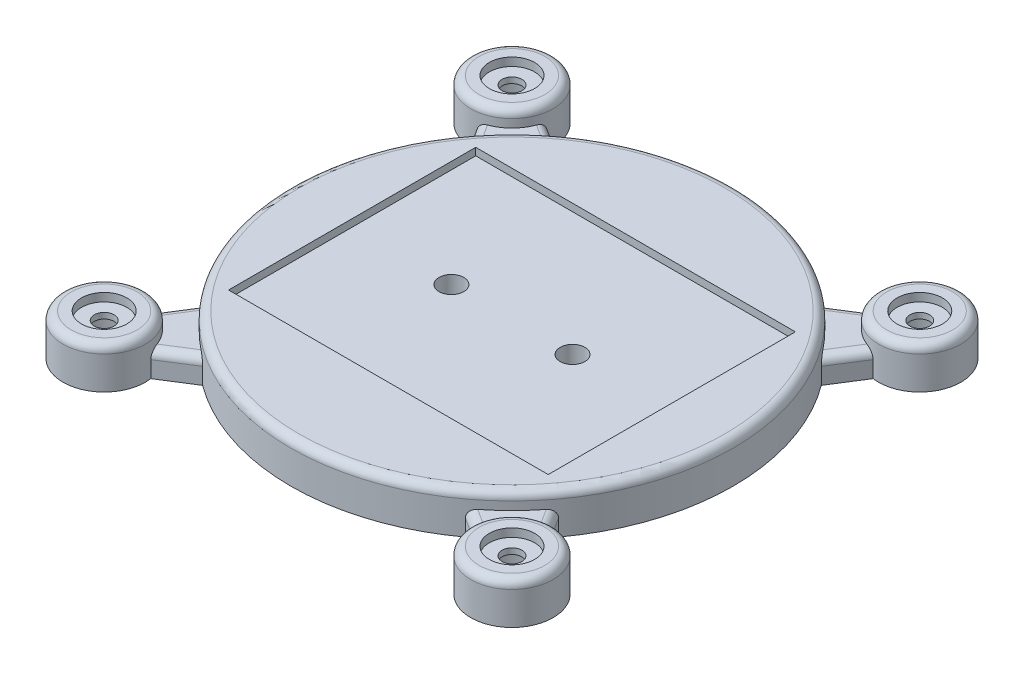
SolidWorks part; units mm, degrees
material "ABS"
ref_plane "Front Plane" through (0, 0, 0) normal (0, 0, 1) x (1, 0, 0)
ref_plane "Top Plane" through (0, 0, 0) normal (0, 1, 0) x (1, 0, 0)
ref_plane "Right Plane" through (0, 0, 0) normal (1, 0, 0) x (0, 0, -1)
sketch "Sketch1" plane through (0, 0, 0) normal (0, 1, 0) x (1, 0, 0)
  circle A0 centre (0, 0) radius 26.85
  dimension "D1" = 53.7
extrude "Boss-Extrude1" add sketch "Sketch1" along normal blind 5
fillet "Fillet1" radius 1 1 edges at (0, 5, 26.85)
sketch "Sketch2" plane through (0, 5, 0) normal (0, 1, 0) x (1, 0, 0)
  line L1 (-19.4, 15) -> (19.4, 15)
  line L2 (-19.4, 15) -> (-19.4, -15)
  line L3 (-19.4, -15) -> (19.4, -15)
  line L4 (19.4, 15) -> (19.4, -15)
  line L5 (-19.4, 15) -> (19.4, -15) construction
  line L6 (-19.4, -15) -> (19.4, 15) construction
  point P0 (0, 0)
  dimension "D1" = 38.8
  dimension "D2" = 30
extrude "Cut-Extrude1" cut sketch "Sketch2" against normal blind 0.9
sketch "Sketch3" plane through (0, 4.1, 0) normal (0, 1, 0) x (1, 0, 0)
  line L0 (-2.75, 0) -> (2.75, 0) construction
  circle A0 centre (7.35, 0) radius 1.5
  circle A1 centre (-7.35, 0) radius 1.5
  dimension "D1" = 3
  dimension "D3" = 3
  dimension "D2" = 7.35
  dimension "D4" = 7.35
extrude "Cut-Extrude2" cut sketch "Sketch3" against normal through all
sketch "Sketch5" plane through (0, 0, 0) normal (0, 1, 0) x (1, 0, 0)
  line L0 (0, 0) -> (24.7487, -24.7487)
  line L1 (-2.75, 0) -> (2.75, 0) construction
  circle A0 centre (24.7487, -24.7487) radius 5
  circle A1 centre (-24.7487, -24.7487) radius 5
  circle A2 centre (-24.7487, 24.7487) radius 5
  circle A3 centre (24.7487, 24.7487) radius 5
  point P15 (0, 0)
  dimension "D2" = 10
  dimension "D1" = 35
  dimension "D3" = 45
  dimension "D4" = 4
sketch "Sketch6" plane through (0, 0, 0) normal (0, 1, 0) x (1, 0, 0)
  line L8 (24.0416, -19.799) -> (21.6024, -15.9455)
  line L9 (19.799, -24.0416) -> (15.9455, -21.6024)
  arc A2 (15.9455, -21.6024) -> (21.6024, -15.9455) centre (0, 0) ccw
  arc A3 (24.0416, -19.799) -> (19.799, -24.0416) centre (24.7487, -24.7487) ccw
  dimension "D2" = 35
  dimension "D1" = 53.7
  dimension "D4" = 10
  dimension "D5" = 8
  dimension "D7" = 6
extrude "Boss-Extrude4" add sketch "Sketch5" along normal blind 5 separate body
extrude "Boss-Extrude5" add sketch "Sketch6" along normal blind 3
fillet "Fillet5" radius 1 2 edges at (22.822, 3, 17.8723) (17.8723, 3, 22.822)
pattern_circular "CirPattern20" count 4 over 360 about axis through (0, 0, 0) along (0, 1, 0) of "Fillet5", "Boss-Extrude5"
fillet "Fillet6" radius 1 1 edges at (-24.7487, 5, -19.7487)
fillet "Fillet7" radius 1 1 edges at (24.7487, 5, -19.7487)
fillet "Fillet8" radius 1 1 edges at (-24.7487, 5, 29.7487)
fillet "Fillet9" radius 1 1 edges at (24.7487, 5, 29.7487)
sketch "Sketch9" plane through (0, 5, 0) normal (0, 1, 0) x (1, 0, 0)
  line L0 (0, 0) -> (24.7487, -24.7487) construction
  line L1 (-2.75, 0) -> (2.75, 0) construction
  circle A0 centre (24.7487, -24.7487) radius 2.75
  circle A1 centre (-24.7487, -24.7487) radius 2.75
  circle A2 centre (-24.7487, 24.7487) radius 2.75
  circle A3 centre (24.7487, 24.7487) radius 2.75
  point P15 (0, 0)
  dimension "D3" = 5.5
  dimension "D1" = 35
  dimension "D2" = 45
  dimension "D4" = 4
extrude "Cut-Extrude5" cut sketch "Sketch9" against normal blind 1
sketch "Sketch10" plane through (0, 4, 0) normal (0, 1, 0) x (1, 0, 0)
  line L0 (0, 0) -> (24.7487, -24.7487) construction
  circle A0 centre (24.7487, -24.7487) radius 1.2
  circle A1 centre (-24.7487, -24.7487) radius 1.2
  circle A2 centre (-24.7487, 24.7487) radius 1.2
  circle A3 centre (24.7487, 24.7487) radius 1.2
  point P14 (0, 0)
  dimension "D1" = 2.4
  dimension "D2" = 4
extrude "Cut-Extrude6" cut sketch "Sketch10" against normal through all
sketch "Sketch11" plane through (0, 0, 0) normal (0, -1, 0) x (1, 0, 0)
  line L0 (0, 0) -> (24.7487, 24.7487) construction
  line L1 (0, -2.75) -> (0, 2.75) construction
  circle A0 centre (24.7487, 24.7487) radius 3.75
  circle A1 centre (24.7487, -24.7487) radius 3.75
  circle A2 centre (-24.7487, -24.7487) radius 3.75
  circle A3 centre (-24.7487, 24.7487) radius 3.75
  point P15 (0, 0)
  dimension "D3" = 7.5
  dimension "D1" = 45
  dimension "D2" = 35
  dimension "D4" = 4
extrude "Cut-Extrude7" cut sketch "Sketch11" against normal blind 3.3
equation "\"D3@Sketch3\"=\"D1@Sketch3\""
equation "\"D4@Sketch3\"=\"D2@Sketch3\""
